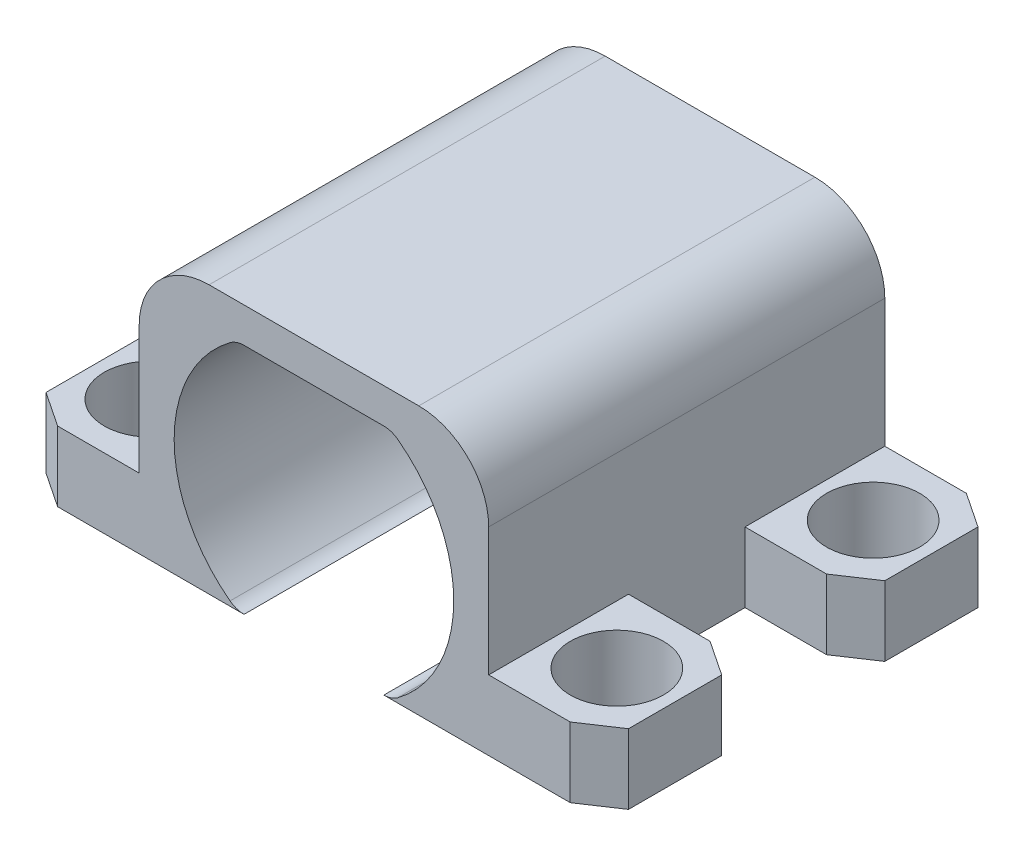
SolidWorks part; units mm, degrees
ref_plane "Ön Düzlem" through (0, 0, 0) normal (0, 0, 1) x (1, 0, 0)
ref_plane "Üst Düzlem" through (0, 0, 0) normal (0, 1, 0) x (1, 0, 0)
ref_plane "Sağ Düzlem" through (0, 0, 0) normal (1, 0, 0) x (0, 0, -1)
sketch "Çizim1" plane through (0, 0, 0) normal (0, 0, 1) x (1, 0, 0)
  line L0 (12, 1) -> (12, 9)
  line L1 (11, 10) -> (1, 10)
  line L2 (0, 9) -> (0, 1)
  line L3 (11, 0) -> (13.5, 0)
  line L4 (13.5, 0) -> (13.5, 8.5)
  line L5 (1, 0) -> (-1.5, 0)
  line L6 (10.5, 11.5) -> (1.5, 11.5)
  line L7 (-1.5, 8.5) -> (-1.5, 0)
  arc A0 (12, 9) -> (11, 10) centre (11, 9) ccw
  arc A1 (1, 10) -> (0, 9) centre (1, 9) ccw
  arc A2 (0, 1) -> (1, 0) centre (1, 1) ccw
  arc A4 (12, 1) -> (11, 0) centre (11, 1) cw
  arc A5 (1.5, 11.5) -> (-1.5, 8.5) centre (1.5, 8.5) ccw
  arc A6 (13.5, 8.5) -> (10.5, 11.5) centre (10.5, 8.5) ccw
  dimension "D4" = 3
  dimension "D5" = 1
  dimension "D6" = 1
  dimension "D7" = 1
  dimension "D8" = 1
  dimension "D11" = 9
  dimension "D1" = 1.5
  dimension "D2" = 1.5
  dimension "D3" = 1.5
  dimension "D9" = 8
  dimension "D10" = 8.5
  dimension "D12" = 10
  dimension "D13" = 8
  dimension "D14" = 2.5
  dimension "D15" = 1.8028
extrude "Yükseklik-Ekstrüzyon1" add sketch "Çizim1" along normal blind 1
sketch "Çizim3" plane through (0, 0, 1) normal (0, 0, 1) x (1, 0, 0)
  line L0 (3, 0) -> (-1.5, 0)
  line L1 (11, 0) -> (1, 0) construction
  line L2 (-1.5, 0) -> (-1.5, 8.5)
  line L3 (9, 0) -> (13.5, 0)
  line L4 (13.5, 0) -> (13.5, 8.5)
  line L5 (10.5, 11.5) -> (1.5, 11.5)
  line L6 (1, 10) -> (11, 10) construction
  line L7 (3, 10) -> (9, 10)
  arc A0 (2.4, 0.2) -> (3, 0) centre (3, 1) ccw construction
  arc A1 (-1.5, 8.5) -> (1.5, 11.5) centre (1.5, 8.5) cw
  arc A2 (10.5, 11.5) -> (13.5, 8.5) centre (10.5, 8.5) cw
  arc A3 (3, 0) -> (2.4, 0.2) centre (3, 1) cw
  arc A4 (2.4, 0.2) -> (2.4, 9.8) centre (6, 5) cw
  arc A5 (2.4, 9.8) -> (3, 10) centre (3, 9) cw
  arc A6 (3, 10) -> (2.4, 9.8) centre (3, 9) ccw construction
  arc A7 (9, 10) -> (9.6, 9.8) centre (9, 9) cw
  arc A8 (9.6, 9.8) -> (9, 10) centre (9, 9) ccw construction
  arc A9 (9.6, 9.8) -> (9.6, 0.2) centre (6, 5) cw
  arc A10 (9, 0) -> (9.6, 0.2) centre (9, 1) ccw
extrude "Yükseklik-Ekstrüzyon2" add sketch "Çizim3" along normal up to vertex (16 mm away)
sketch "Çizim4" plane through (0, 0, 0) normal (0, -1, 0) x (1, 0, 0)
  line L0 (13.5, 8.5) -> (-1.5, 8.5) construction
  line L1 (13.5, 0) -> (13.5, 6)
  line L2 (13.5, 17) -> (13.5, 0) construction
  line L3 (-1.5, 17) -> (-1.5, 0) construction
  line L4 (13.5, 6) -> (17, 6)
  line L5 (13.5, 17) -> (17, 17)
  line L6 (17, 17) -> (18.5, 16)
  line L7 (6, 17) -> (6, 0) construction
  line L8 (10.5, 17) -> (1.5, 17) construction
  line L9 (10.5, 0) -> (1.5, 0) construction
  line L10 (18.5, 12) -> (18.5, 16)
  line L11 (17, 11) -> (18.5, 12)
  line L12 (13.5, 11) -> (17, 11)
  line L13 (13.5, 17) -> (13.5, 11)
  line L14 (17, 6) -> (18.5, 5)
  line L15 (18.5, 5) -> (18.5, 1)
  line L16 (17, 0) -> (18.5, 1)
  line L17 (13.5, 0) -> (17, 0)
  line L18 (-1.5, 0) -> (-5, 0)
  line L19 (-5, 0) -> (-6.5, 1)
  line L20 (-6.5, 5) -> (-6.5, 1)
  line L21 (-5, 6) -> (-6.5, 5)
  line L22 (-1.5, 17) -> (-1.5, 11)
  line L23 (-1.5, 11) -> (-5, 11)
  line L24 (-5, 11) -> (-6.5, 12)
  line L25 (-6.5, 12) -> (-6.5, 16)
  line L26 (-5, 17) -> (-6.5, 16)
  line L27 (-1.5, 17) -> (-5, 17)
  line L28 (-1.5, 6) -> (-5, 6)
  line L29 (-1.5, 0) -> (-1.5, 6)
  line L30 (18.5, 14) -> (13.5, 14) construction
  line L31 (18.5, 3) -> (13.5, 3) construction
  line L32 (-6.5, 3) -> (-1.5, 3) construction
  line L33 (-6.5, 14) -> (-1.5, 14) construction
  circle A0 centre (16, 14) radius 2
  circle A1 centre (16, 3) radius 2
  circle A2 centre (-4, 3) radius 2
  circle A3 centre (-4, 14) radius 2
  dimension "D5" = 3.5
  dimension "D6" = 4
  dimension "D1" = 4
  dimension "D2" = 6
  dimension "D3" = 5
  dimension "D4" = 1.5
  dimension "D7" = 2.5
extrude "Yükseklik-Ekstrüzyon3" add sketch "Çizim4" against normal blind 3
